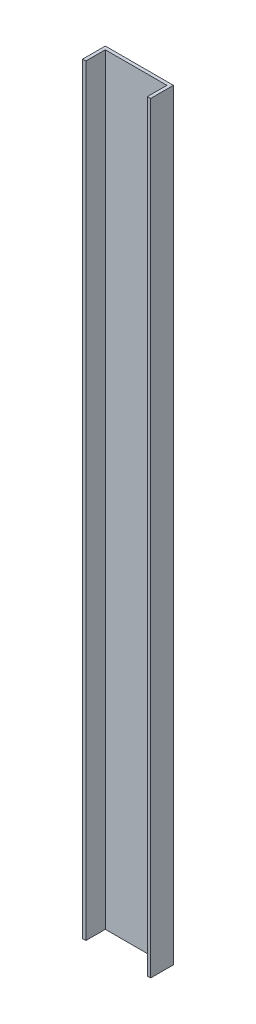
SolidWorks part; units mm, degrees
ref_plane "Front Plane" through (0, 0, 0) normal (0, 0, 1) x (1, 0, 0)
ref_plane "Top Plane" through (0, 0, 0) normal (0, 1, 0) x (1, 0, 0)
ref_plane "Right Plane" through (0, 0, 0) normal (1, 0, 0) x (0, 0, -1)
ref_plane "Plane1" through (0, 2350, 0) normal (0, 1, 0) x (1, 0, 0)
sketch "Sketch1" plane through (0, 2350, 0) normal (0, 1, 0) x (1, 0, 0)
  line L0 (-10, 70) -> (-10, 0)
  line L1 (-10, 0) -> (0, 0)
  line L2 (0, 0) -> (0, 60)
  line L3 (0, 60) -> (190, 60)
  line L4 (190, 60) -> (190, 0)
  line L5 (190, 0) -> (200, 0)
  line L6 (200, 0) -> (200, 70)
  line L7 (200, 70) -> (-10, 70)
extrude "Boss-Extrude1" add sketch "Sketch1" against normal blind 2350
